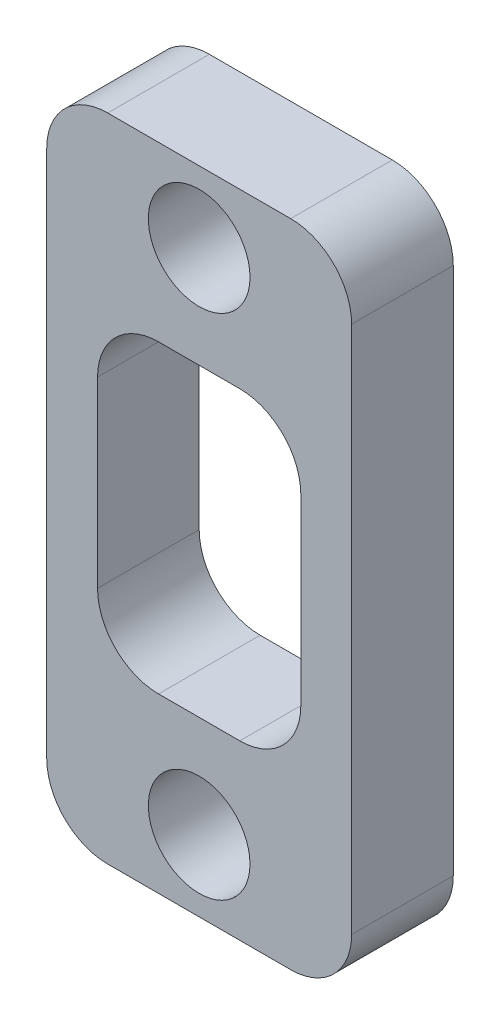
SolidWorks part; units mm, degrees
material "瞎编数据的PLA"
ref_plane "前视基准面" through (0, 0, 0) normal (0, 0, 1) x (1, 0, 0)
ref_plane "上视基准面" through (0, 0, 0) normal (0, 1, 0) x (1, 0, 0)
ref_plane "右视基准面" through (0, 0, 0) normal (1, 0, 0) x (0, 0, -1)
sketch "草图1" plane through (0, 0, 0) normal (0, 0, 1) x (1, 0, 0)
  line L0 (0, 0) -> (0, 25) construction
  line L2 (-7.5, 28.5) -> (7.5, 28.5)
  line L3 (-7.5, 28.5) -> (-7.5, -3.5)
  line L4 (-7.5, -3.5) -> (7.5, -3.5)
  line L5 (7.5, 28.5) -> (7.5, -3.5)
  line L6 (-7.5, 28.5) -> (7.5, -3.5) construction
  line L7 (-7.5, -3.5) -> (7.5, 28.5) construction
  line L8 (-5, 20) -> (5, 20)
  line L9 (-5, 20) -> (-5, 5)
  line L10 (-5, 5) -> (5, 5)
  line L11 (5, 20) -> (5, 5)
  line L12 (-5, 20) -> (5, 5) construction
  line L13 (-5, 5) -> (5, 20) construction
  circle A0 centre (0, 25) radius 2.5
  circle A1 centre (0, 0) radius 2.5
  point P5 (0, 12.5)
  point P10 (0, 12.5)
  dimension "D1" = 5
  dimension "D2" = 25
  dimension "D3" = 15
  dimension "D4" = 32
  dimension "D5" = 15
  dimension "D6" = 10
extrude "凸台-拉伸1" add sketch "草图1" along normal blind 5
fillet "圆角1" radius 3 8 edges at (-7.5, -3.5, 2.5) (7.5, -3.5, 2.5) (7.5, 28.5, 2.5) (-7.5, 28.5, 2.5) (-5, 5, 2.5) (5, 5, 2.5) (5, 20, 2.5) (-5, 20, 2.5)
